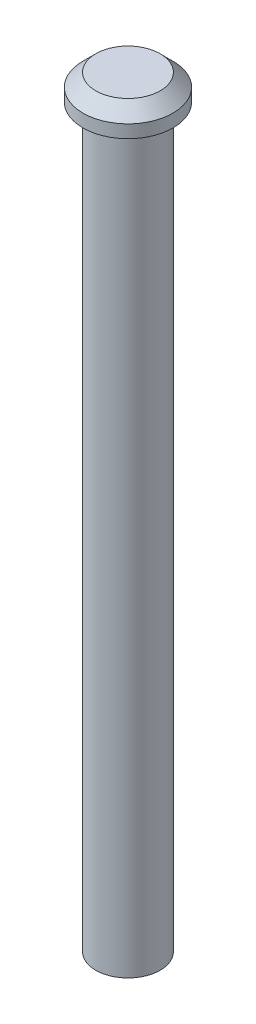
SolidWorks part; units mm, degrees
ref_plane "Front Plane" through (0, 0, 0) normal (0, 0, 1) x (1, 0, 0)
ref_plane "Top Plane" through (0, 0, 0) normal (0, 1, 0) x (1, 0, 0)
ref_plane "Right Plane" through (0, 0, 0) normal (1, 0, 0) x (0, 0, -1)
sketch "Sketch1" plane through (0, 0, 0) normal (0, 1, 0) x (1, 0, 0)
  circle A0 centre (0, 0) radius 2.5
  dimension "D1" = 5
extrude "Boss-Extrude1" add sketch "Sketch1" along normal blind 57.2
sketch "Sketch2" plane through (0, 57.2, 0) normal (0, 1, 0) x (1, 0, 0)
  circle A0 centre (0, 0) radius 3.5
  dimension "D1" = 7
extrude "Boss-Extrude2" add sketch "Sketch2" along normal blind 2
chamfer "Chamfer1" distance 1 angle 45 1 edges at (0, 59.2, 3.5)
sketch "Sketch3" plane through (0, 0, 0) normal (0, -1, 0) x (1, 0, 0)
  circle A0 centre (0, 0) radius 1.5
  dimension "D1" = 3
extrude "Cut-Extrude1" cut sketch "Sketch3" against normal blind 5
